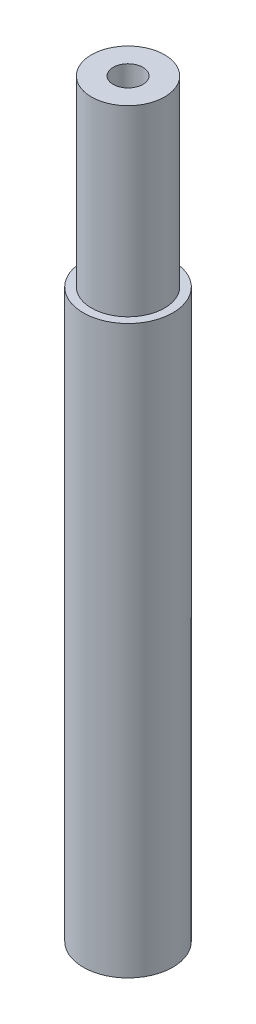
SolidWorks part; units mm, degrees
ref_plane "Front Plane" through (0, 0, 0) normal (0, 0, 1) x (1, 0, 0)
ref_plane "Top Plane" through (0, 0, 0) normal (0, 1, 0) x (1, 0, 0)
ref_plane "Right Plane" through (0, 0, 0) normal (1, 0, 0) x (0, 0, -1)
sketch "Sketch1" plane through (0, 0, 0) normal (0, 1, 0) x (1, 0, 0)
  circle A0 centre (0, 0) radius 4
  circle A2 centre (0, 0) radius 1.625
  dimension "D1" = 8
  dimension "D2" = 3.25
extrude "Boss-Extrude2" add sketch "Sketch1" along normal blind 20
sketch "Sketch2" plane through (0, 0, 0) normal (0, -1, 0) x (1, 0, 0)
  circle A0 centre (0, 0) radius 4.9
  dimension "D1" = 9.8
extrude "Boss-Extrude3" add sketch "Sketch2" along normal blind 62
sketch "Sketch6" plane through (0, -62, 0) normal (0, -1, 0) x (1, 0, 0)
  circle A0 centre (0, 0) radius 1.625
  dimension "D1" = 3.25
extrude "Cut-Extrude3" cut sketch "Sketch6" against normal blind 20
